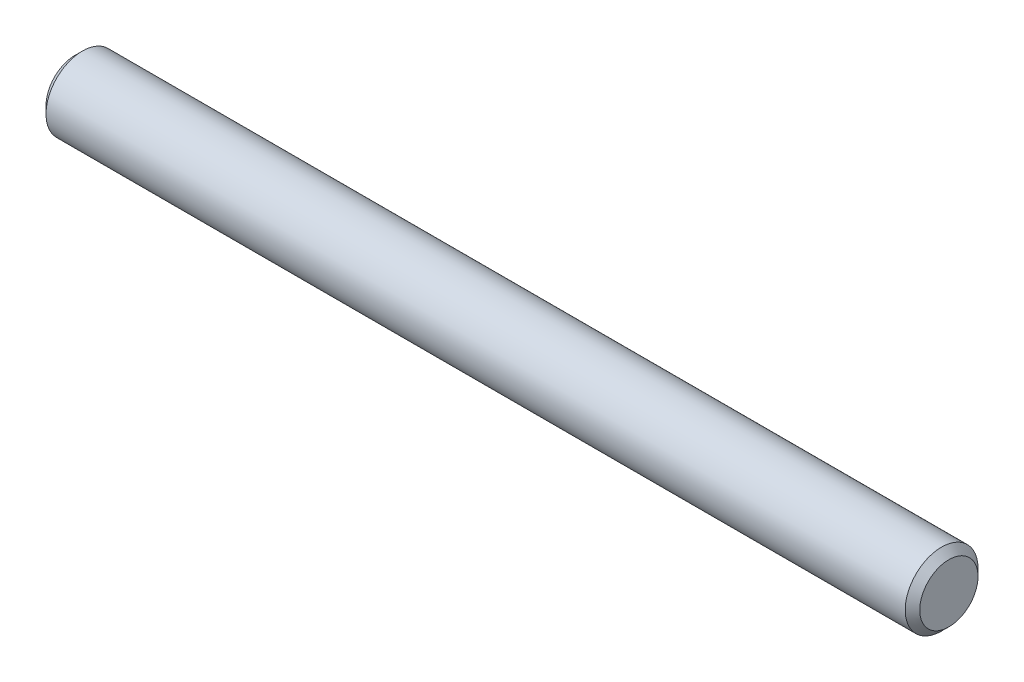
SolidWorks part; units mm, degrees
ref_plane "Front" through (0, 0, 0) normal (0, 0, 1) x (1, 0, 0)
ref_plane "Top" through (0, 0, 0) normal (0, 1, 0) x (1, 0, 0)
ref_plane "Right" through (0, 0, 0) normal (1, 0, 0) x (0, 0, -1)
sketch "Sketch1" plane through (0, 0, 0) normal (0, 0, 1) x (1, 0, 0)
  line L0 (-19.05, 0) -> (19.05, 0) construction
  line L1 (19.05, 1.5875) -> (19.05, -1.5875) construction
  line L2 (-19.05, 1.5875) -> (-19.05, -1.5875) construction
  dimension "Length" = 38.1
  dimension "Diameter" = 3.175
sketch "Sketch2" plane through (0, 0, 0) normal (1, 0, 0) x (0, 0, -1)
  circle A0 centre (0, 0) radius 1.5875
extrude "Extrude1" add sketch "Sketch2" against normal up to vertex (19.05 mm away) and the other way up to vertex (19.05 mm away) up to point (-19.05, 1.5875, 0) other way up to point (19.05, 1.5875, 0)
chamfer "Chamfer1" distance 0.3175 angle 45 2 edges at (19.05, 0, -1.5875) (-19.05, 0, -1.5875)
equation "\"D1@Chamfer1\" = \"Diameter@Sketch1\"*.1"
